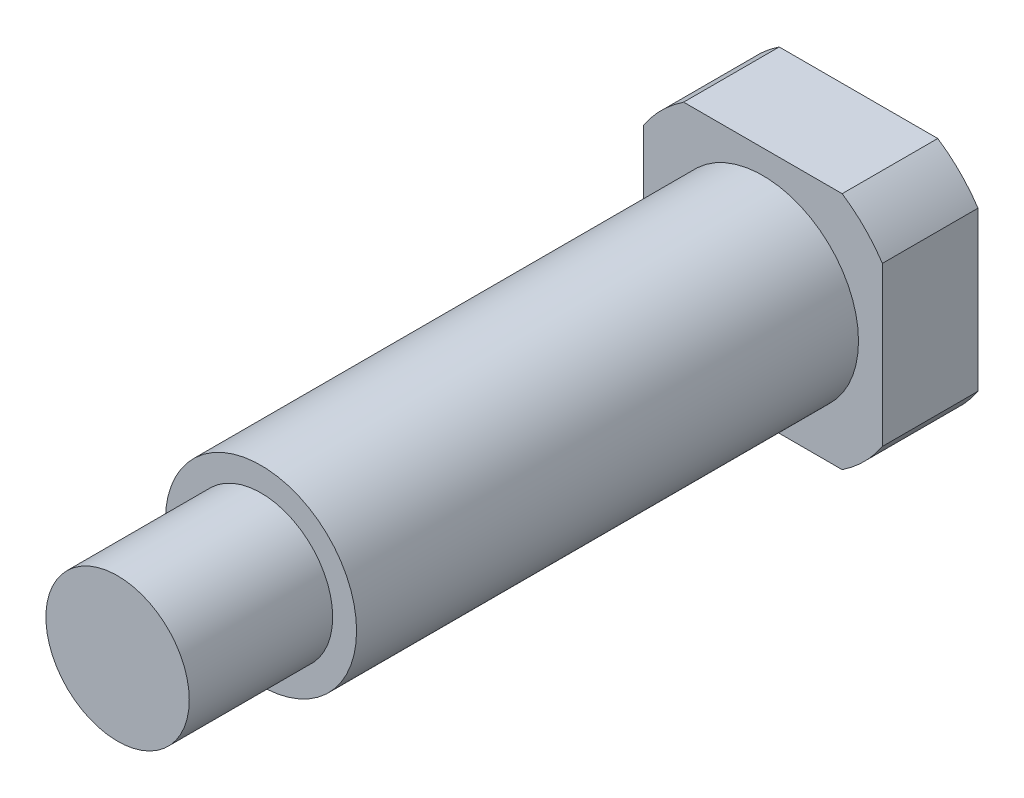
SolidWorks part; units mm, degrees
ref_plane "前视基准面" through (0, 0, 0) normal (0, 0, 1) x (1, 0, 0)
ref_plane "上视基准面" through (0, 0, 0) normal (0, 1, 0) x (1, 0, 0)
ref_plane "右视基准面" through (0, 0, 0) normal (1, 0, 0) x (0, 0, -1)
sketch "草图1" plane through (0, 0, 0) normal (0, 0, 1) x (1, 0, 0)
  circle A0 centre (0, 0) radius 6
  dimension "D1" = 12
extrude "凸台-拉伸1" add sketch "草图1" along normal blind 4
sketch "草图2" plane through (0, 0, 4) normal (0, 0, 1) x (1, 0, 0)
  circle A0 centre (0, 0) radius 4
  dimension "D1" = 8
extrude "凸台-拉伸2" add sketch "草图2" along normal blind 21
sketch "草图3" plane through (0, 0, 25) normal (0, 0, 1) x (1, 0, 0)
  circle A0 centre (0, 0) radius 3
  dimension "D1" = 6
extrude "凸台-拉伸3" add sketch "草图3" along normal blind 6
cosmetic thread "装饰螺纹线1" parameters "D2"=5
sketch "草图4" plane through (0, 0, 0) normal (0, 0, -1) x (-1, 0, 0)
  line L1 (5, 5) -> (-5, 5)
  line L2 (5, 5) -> (5, -5)
  line L3 (5, -5) -> (-5, -5)
  line L4 (-5, 5) -> (-5, -5)
  line L5 (5, 5) -> (-5, -5) construction
  line L6 (5, -5) -> (-5, 5) construction
  circle A0 centre (0, 0) radius 7.5
  point P0 (0, 0)
  dimension "D1" = 10
  dimension "D2" = 10
extrude "切除-拉伸1" cut sketch "草图4" against normal blind 6
